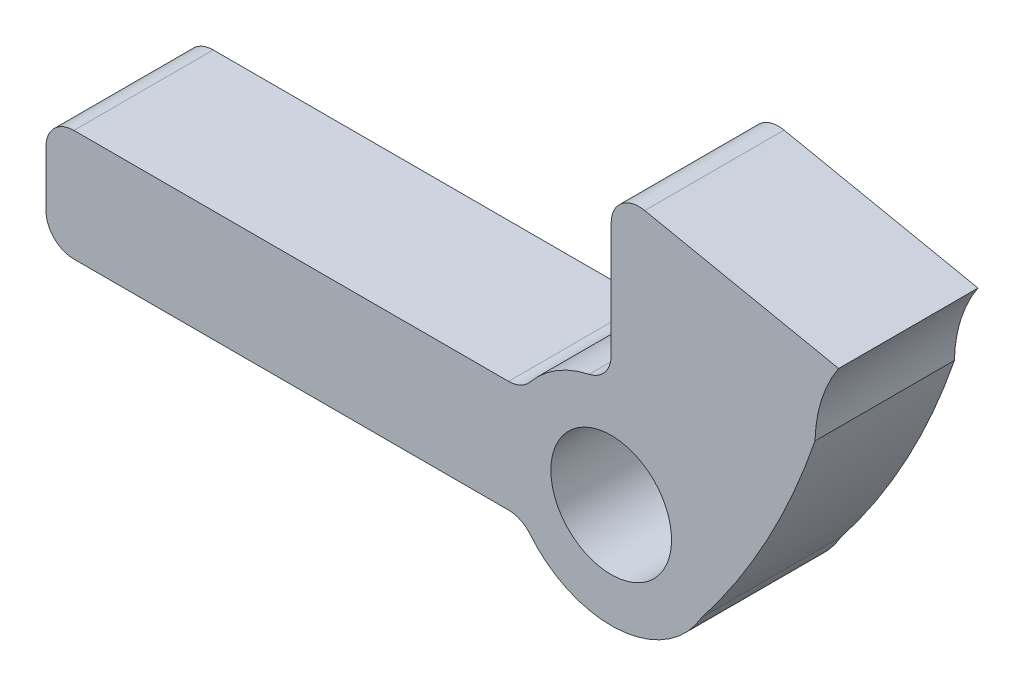
SolidWorks part; units mm, degrees
ref_plane "Front Plane" through (0, 0, 0) normal (0, 0, 1) x (1, 0, 0)
ref_plane "Top Plane" through (0, 0, 0) normal (0, 1, 0) x (1, 0, 0)
ref_plane "Right Plane" through (0, 0, 0) normal (1, 0, 0) x (0, 0, -1)
sketch "Sketch1" plane through (0, 0, 0) normal (0, 0, 1) x (1, 0, 0)
  line L1 (0, 0) -> (50, 0)
  line L2 (0, 0) -> (0, 50)
  line L3 (0, 50) -> (50, 50)
  line L4 (50, 0) -> (50, 50)
  dimension "D1" = 50
  dimension "D2" = 50
extrude "Boss-Extrude1" add sketch "Sketch1" along normal blind 6.35
sketch "Sketch2" plane through (0, 0, 0) normal (0, 0, -1) x (-1, 0, 0)
  line L6 (-26.8508, 24.3777) -> (-7.0423, 24.3777)
  line L7 (-5.7723, 28.1877) -> (-5.7723, 25.6477)
  line L8 (-26.8508, 29.4577) -> (-7.0423, 29.4577)
  line L9 (-31.5279, 38.0574) -> (-31.5279, 32.815)
  line L10 (-41.8934, 37.4859) -> (-33.0557, 39.301)
  arc A12 (-35.6523, 24.5365) -> (-27.8355, 23.9098) centre (-31.5279, 26.9177) ccw
  arc A13 (-26.8508, 24.3777) -> (-27.8355, 23.9098) centre (-26.8508, 23.1077) ccw
  arc A14 (-7.0423, 24.3777) -> (-5.7723, 25.6477) centre (-7.0423, 25.6477) ccw
  arc A15 (-5.7723, 28.1877) -> (-7.0423, 29.4577) centre (-7.0423, 28.1877) ccw
  arc A16 (-27.8355, 29.9256) -> (-26.8508, 29.4577) centre (-26.8508, 30.7277) ccw
  arc A17 (-27.8355, 29.9256) -> (-30.5253, 31.5735) centre (-31.5279, 26.9177) ccw
  arc A18 (-31.5279, 32.815) -> (-30.5253, 31.5735) centre (-30.2579, 32.815) ccw
  arc A19 (-31.5279, 38.0574) -> (-33.0557, 39.301) centre (-32.7979, 38.0574) ccw
  arc A22 (-40.8162, 34.0889) -> (-41.8934, 37.4859) centre (-47.1646, 33.9452) ccw
  arc A23 (-40.8162, 34.0889) -> (-35.6523, 24.5365) centre (-9.9687, 44.5925) ccw
  circle A25 centre (-31.5279, 26.9177) radius 2.75
  point P21 (-41.4805, 37.6138)
  point P22 (-41.4805, 37.5445)
  point P23 (-40.8162, 34.0889)
  point P24 (-41.8934, 37.4859)
  point P26 (0, 0)
  point P30 (0, 0)
  dimension "D1" = 5.5
extrude "Cut-Extrude1" cut sketch "Sketch2" against normal through all flip side to cut
